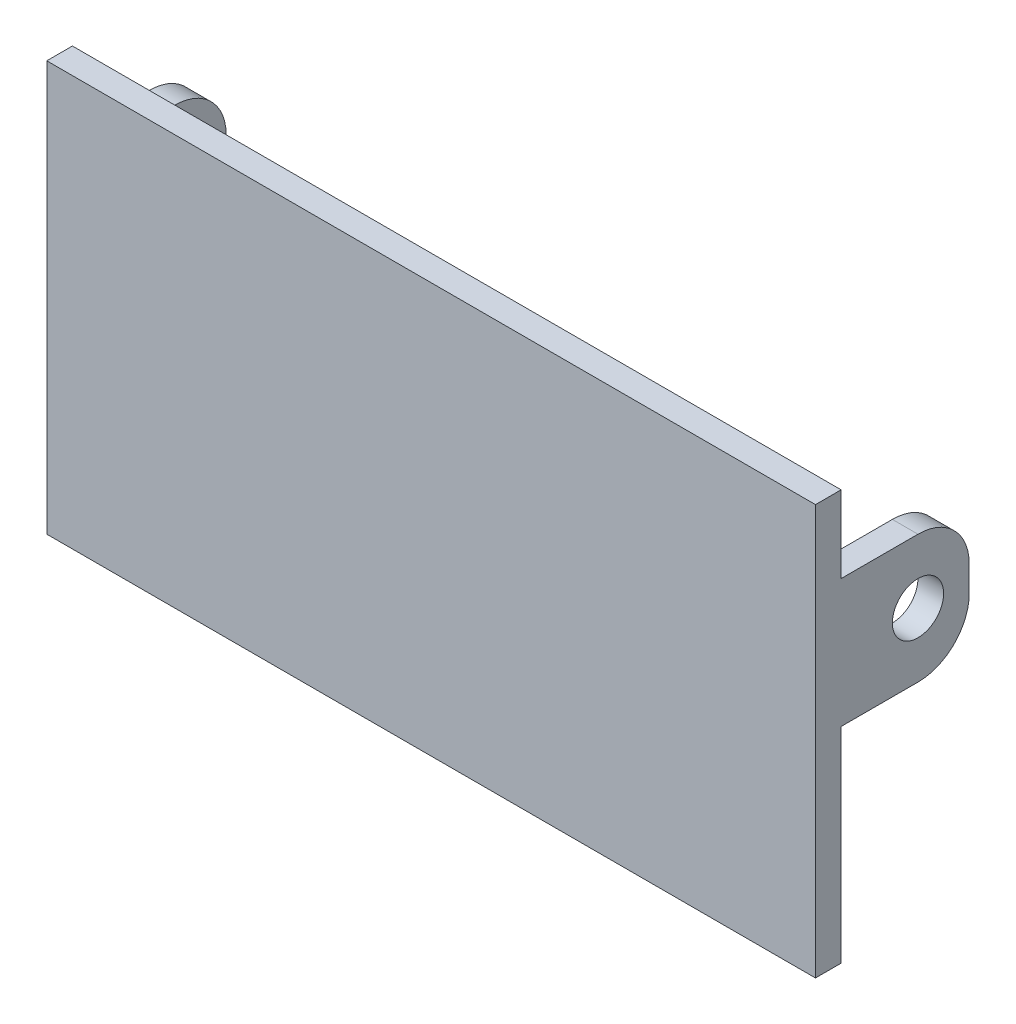
SolidWorks part; units mm, degrees
ref_plane "Front Plane" through (0, 0, 0) normal (0, 0, 1) x (1, 0, 0)
ref_plane "Top Plane" through (0, 0, 0) normal (0, 1, 0) x (1, 0, 0)
ref_plane "Right Plane" through (0, 0, 0) normal (1, 0, 0) x (0, 0, -1)
sketch "Sketch1" plane through (0, 0, 0) normal (0, 0, 1) x (1, 0, 0)
  line L1 (0, 0) -> (-150, 0)
  line L2 (0, 0) -> (0, 80)
  line L3 (0, 80) -> (-150, 80)
  line L4 (-150, 0) -> (-150, 80)
  dimension "D1" = 150
  dimension "D2" = 80
extrude "Boss-Extrude1" add sketch "Sketch1" along normal blind 5 contours L3 L4 L1 L2
sketch "Sketch2" plane through (0, 0, 0) normal (0, 0, -1) x (-1, 0, 0)
  line L0 (0, 0) -> (0, 80) construction
  line L1 (75, 0) -> (75, 80) construction
  line L2 (0, 0) -> (150, 0) construction
  line L3 (0, 80) -> (150, 80) construction
  line L4 (0, 65) -> (5, 65)
  line L5 (0, 65) -> (0, 40)
  line L6 (0, 40) -> (5, 40)
  line L7 (5, 65) -> (5, 40)
  line L8 (150, 40) -> (145, 40)
  line L9 (145, 65) -> (145, 40)
  line L10 (150, 65) -> (145, 65)
  line L11 (150, 65) -> (150, 40)
  dimension "D1" = 40
  dimension "D2" = 5
  dimension "D3" = 25
extrude "Boss-Extrude2" add sketch "Sketch2" along normal blind 25
sketch "Sketch3" plane through (0, 0, 0) normal (1, 0, 0) x (0, 0, -1)
  line L3 (25, 52.5) -> (-5, 52.5) construction
  line L4 (25, 65) -> (25, 40) construction
  line L5 (-5, 0) -> (-5, 80) construction
  circle A1 centre (15, 52.5) radius 5
  dimension "D1" = 10
  dimension "D2" = 10
extrude "Cut-Extrude1" cut sketch "Sketch3" against normal through all
fillet "Fillet1" radius 10 4 edges at (-147.5, 65, -25) (-147.5, 40, -25) (-2.5, 65, -25) (-2.5, 40, -25)
